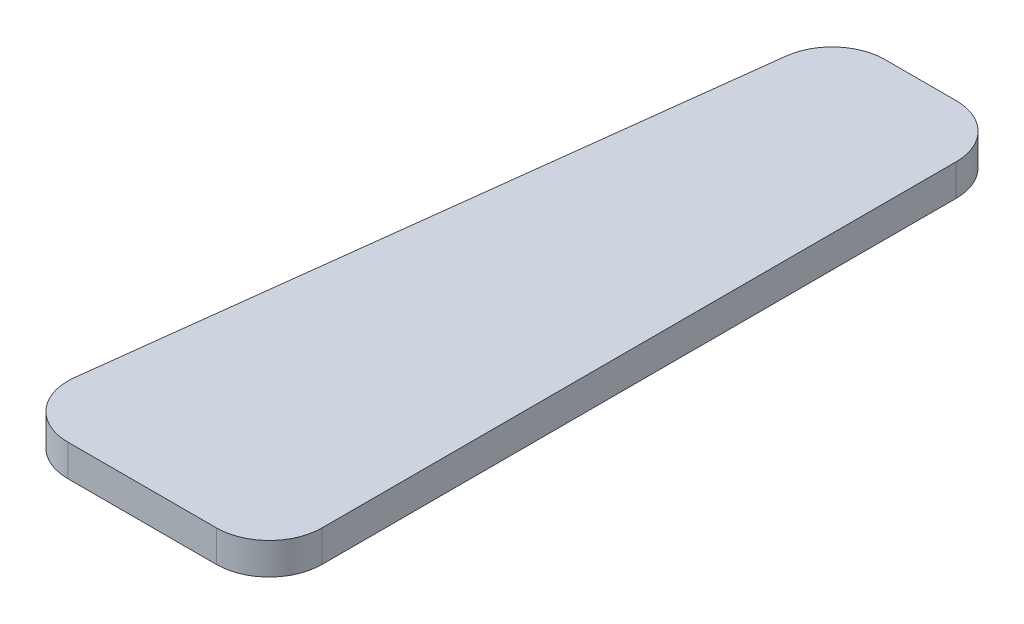
SolidWorks part; units mm, degrees
ref_plane "Front Plane" through (0, 0, 0) normal (0, 0, 1) x (1, 0, 0)
ref_plane "Top Plane" through (0, 0, 0) normal (0, 1, 0) x (1, 0, 0)
ref_plane "Right Plane" through (0, 0, 0) normal (1, 0, 0) x (0, 0, -1)
sketch "Sketch1" plane through (0, 0, 0) normal (0, 1, 0) x (1, 0, 0)
  line L0 (-3.6518, 29.7853) -> (-10.9689, -30.2147)
  line L1 (-6.0056, -35.82) -> (8.0555, -35.82)
  line L2 (13.0555, -30.82) -> (13.0555, 29.18)
  line L3 (8.0555, 34.18) -> (1.3114, 34.18)
  arc A0 (-6.0056, -35.82) -> (-10.9689, -30.2147) centre (-6.0056, -30.82) cw
  arc A1 (8.0555, -35.82) -> (13.0555, -30.82) centre (8.0555, -30.82) ccw
  arc A2 (13.0555, 29.18) -> (8.0555, 34.18) centre (8.0555, 29.18) ccw
  arc A3 (1.3114, 34.18) -> (-3.6518, 29.7853) centre (1.3114, 29.18) ccw
  point P12 (1.0249, -35.82)
  dimension "D1" = 70
extrude "Boss-Extrude1" add sketch "Sketch1" along normal blind 3
